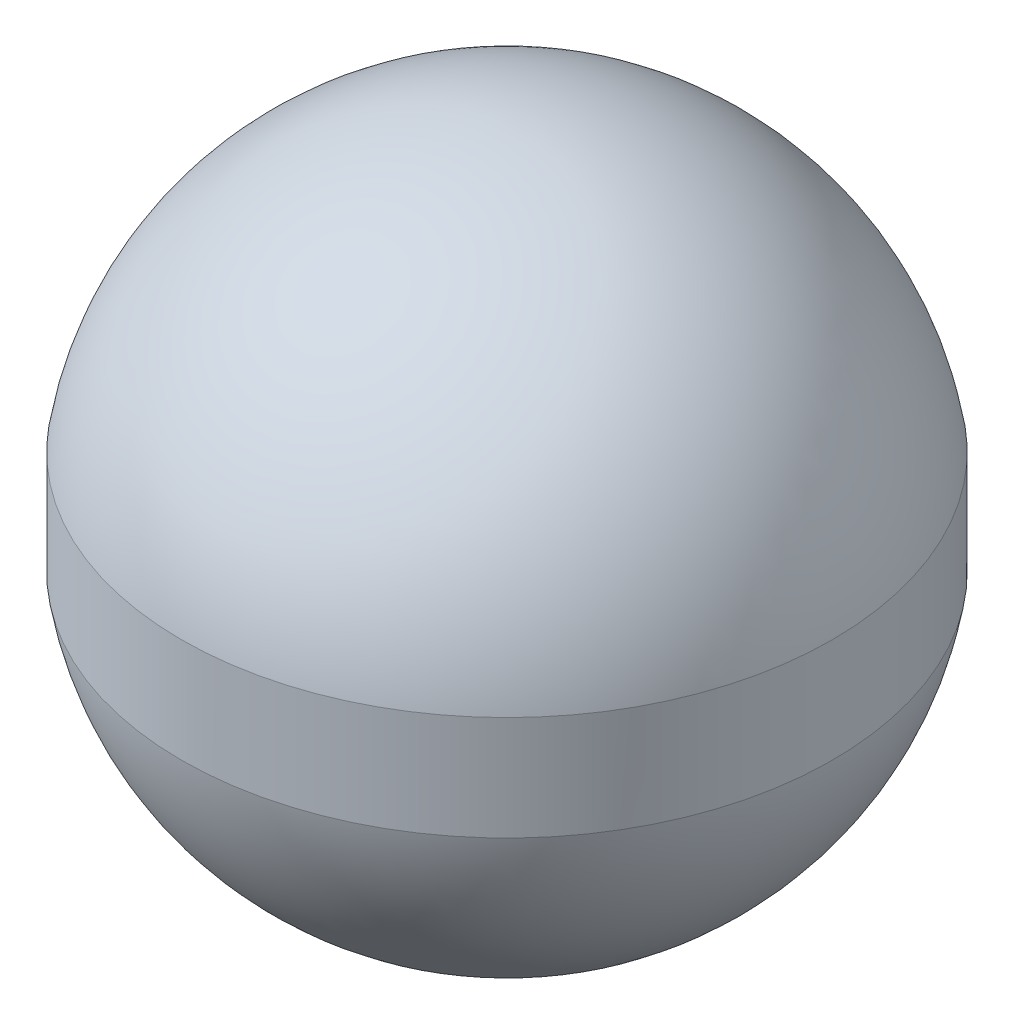
SolidWorks part; units mm, degrees
material "Polyetheretherketone (PEEK)"
ref_plane "Front Plane" through (0, 0, 0) normal (0, 0, 1) x (1, 0, 0)
ref_plane "Top Plane" through (0, 0, 0) normal (0, 1, 0) x (1, 0, 0)
ref_plane "Right Plane" through (0, 0, 0) normal (1, 0, 0) x (0, 0, -1)
sketch "Sketch1" plane through (0, 0, 0) normal (0, 0, 1) x (1, 0, 0)
  line L0 (0, 7.9375) -> (0, -7.9375)
  line L1 (7.8375, 1.256) -> (7.8375, -1.256)
  line L2 (0, -7.9365) -> (0.126, -7.9365)
  arc A0 (0, -7.9375) -> (0, 7.9375) centre (0, 0) ccw
  point P1 (7.9375, 0)
  dimension "D1" = 7.9375
  dimension "D2" = 7.8375
  dimension "D3" = 0.001
revolve "Revolve1" add sketch "Sketch1" angle 360 about L0
equation "\"D1@Sketch1\"=(0.625in)/2"
equation "\"D2@Sketch1\"=\"D1@Sketch1\"-0.1"
